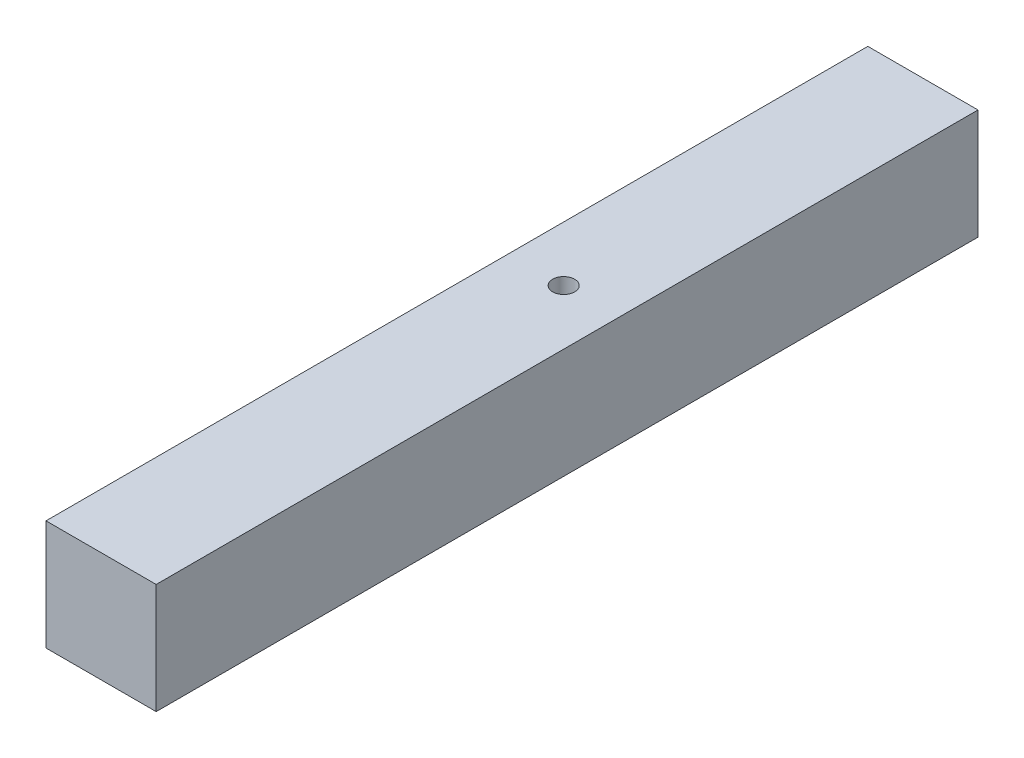
SolidWorks part; units mm, degrees
ref_plane "Front Plane" through (0, 0, 0) normal (0, 0, 1) x (1, 0, 0)
ref_plane "Top Plane" through (0, 0, 0) normal (0, 1, 0) x (1, 0, 0)
ref_plane "Right Plane" through (0, 0, 0) normal (1, 0, 0) x (0, 0, -1)
sketch "Sketch1" plane through (0, 0, 0) normal (0, 0, 1) x (1, 0, 0)
  line L1 (0, 0) -> (20, 0)
  line L2 (0, 0) -> (0, 20)
  line L3 (0, 20) -> (20, 20)
  line L4 (20, 0) -> (20, 20)
  dimension "D1" = 20
  dimension "D2" = 20
extrude "Boss-Extrude1" add sketch "Sketch1" along normal blind 149.19
sketch "Sketch2" plane through (0, 20, 0) normal (0, 1, 0) x (1, 0, 0)
  line L0 (0, 0) -> (0, -149.19) construction
  line L1 (0, -65.2145) -> (23.9363, -65.2145) construction
  line L2 (10, 0) -> (10, -149.19) construction
  line L3 (0, 0) -> (20, 0) construction
  line L4 (0, -149.19) -> (20, -149.19) construction
  circle A0 centre (10, -65.2145) radius 2
  dimension "D1" = 4
extrude "Cut-Extrude1" cut sketch "Sketch2" against normal through all
